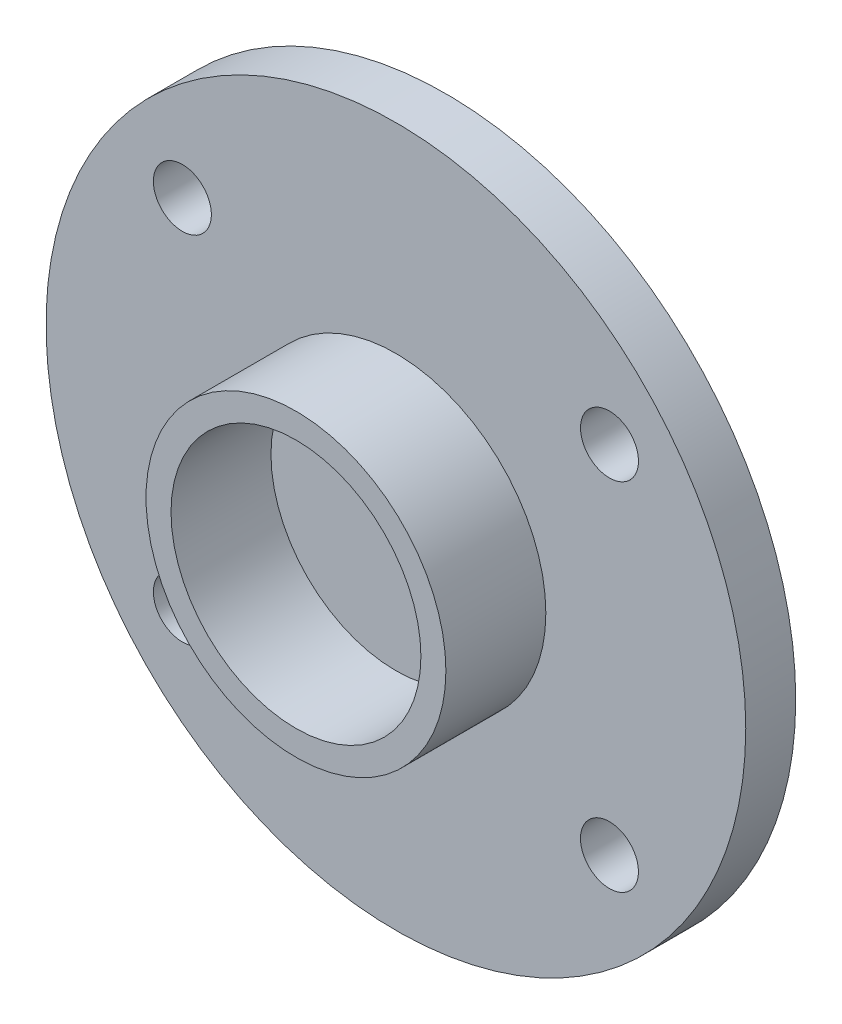
SolidWorks part; units mm, degrees
material "ABS"
ref_plane "Front Plane" through (0, 0, 0) normal (0, 0, 1) x (1, 0, 0)
ref_plane "Top Plane" through (0, 0, 0) normal (0, 1, 0) x (1, 0, 0)
ref_plane "Right Plane" through (0, 0, 0) normal (1, 0, 0) x (0, 0, -1)
sketch "Sketch2" plane through (0, 0, 0) normal (0, 0, 1) x (1, 0, 0)
  line L0 (0, 7) -> (0, -7) construction
  line L1 (0, 0) -> (4.2729, 3.5575) construction
  line L2 (-7, 0) -> (7, 0) construction
  line L3 (0, 0) -> (-4.2729, 3.5575) construction
  circle A0 centre (0, 0) radius 7
  circle A1 centre (4.2729, 3.5575) radius 0.58
  circle A2 centre (-4.2729, 3.5575) radius 0.58
  circle A3 centre (4.2729, -3.5575) radius 0.58
  circle A4 centre (-4.2729, -3.5575) radius 0.58
  dimension "D1" = 14
  dimension "D2" = 5.56
  dimension "D3" = 50.22
extrude "Boss-Extrude1" add sketch "Sketch2" along normal blind 1
sketch "Sketch3" plane through (0, 0, 1) normal (0, 0, 1) x (1, 0, 0)
  circle A0 centre (0, 0) radius 2.5
  dimension "D1" = 5
extrude "Extrude-Thin1" add sketch "Sketch3" along normal blind 2 thin
